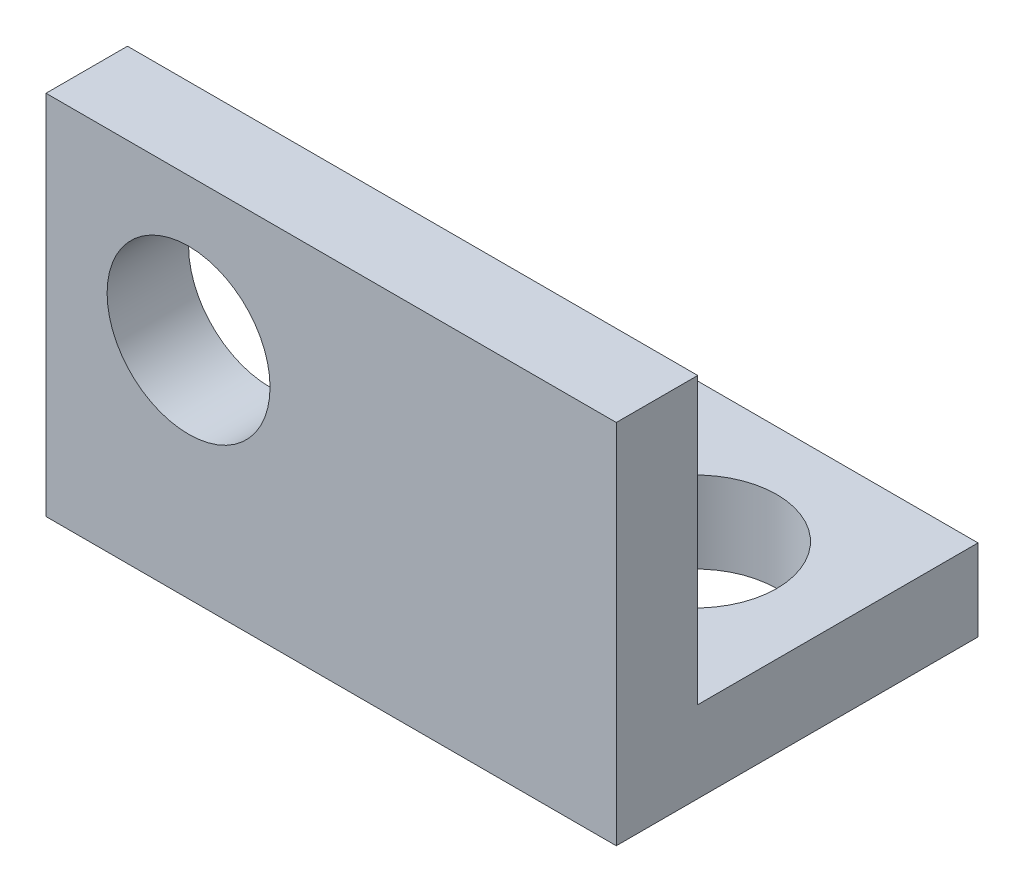
SolidWorks part; units mm, degrees
ref_plane "Front Plane" through (0, 0, 0) normal (0, 0, 1) x (1, 0, 0)
ref_plane "Top Plane" through (0, 0, 0) normal (0, 1, 0) x (1, 0, 0)
ref_plane "Right Plane" through (0, 0, 0) normal (1, 0, 0) x (0, 0, -1)
sketch "Sketch1" plane through (0, 0, 0) normal (0, 1, 0) x (1, 0, 0)
  line L0 (-4.445, -4.3688) -> (-4.445, -11.2776) construction
  line L1 (0, 0) -> (-8.89, 0)
  line L2 (0, 0) -> (0, -11.2776)
  line L3 (0, -11.2776) -> (-8.89, -11.2776)
  line L4 (-8.89, 0) -> (-8.89, -11.2776)
  line L5 (0, -5.6388) -> (-8.89, -5.6388) construction
  circle A0 centre (-4.445, -4.3688) radius 2.54
  dimension "D3" = 5.08
  dimension "D2" = 8.89
  dimension "D1" = 11.2776
  dimension "D4" = 6.9088
extrude "Boss-Extrude1" add sketch "Sketch1" along normal blind 2.54
sketch "Sketch4" plane through (0, 0, 11.2776) normal (0, 0, 1) x (1, 0, 0)
  line L0 (-8.89, 2.54) -> (0, 2.54) construction
  line L1 (0, 0) -> (-17.78, 0)
  line L2 (0, 0) -> (0, 11.43)
  line L3 (0, 11.43) -> (-17.78, 11.43)
  line L4 (-17.78, 0) -> (-17.78, 11.43)
  line L5 (-8.89, 2.54) -> (0, 2.54) construction
  line L6 (-13.335, 6.985) -> (-13.335, 11.43) construction
  line L7 (-13.335, 6.985) -> (-17.78, 6.985) construction
  circle A0 centre (-13.335, 6.985) radius 2.54
  dimension "D3" = 5.08
  dimension "D1" = 17.78
  dimension "D2" = 11.43
  dimension "D4" = 4.445
  dimension "D5" = 4.445
extrude "Boss-Extrude2" add sketch "Sketch4" against normal blind 2.54
equation "\"D4@Sketch1\"=0.272"
equation "\"D1@Sketch1\"=\"D4@Sketch1\"*2-.1"
equation "\"D4@Sketch4\"=(\"D2@Sketch4\"-.1)/2"
equation "\"D5@Sketch4\"=\"D4@Sketch4\""
